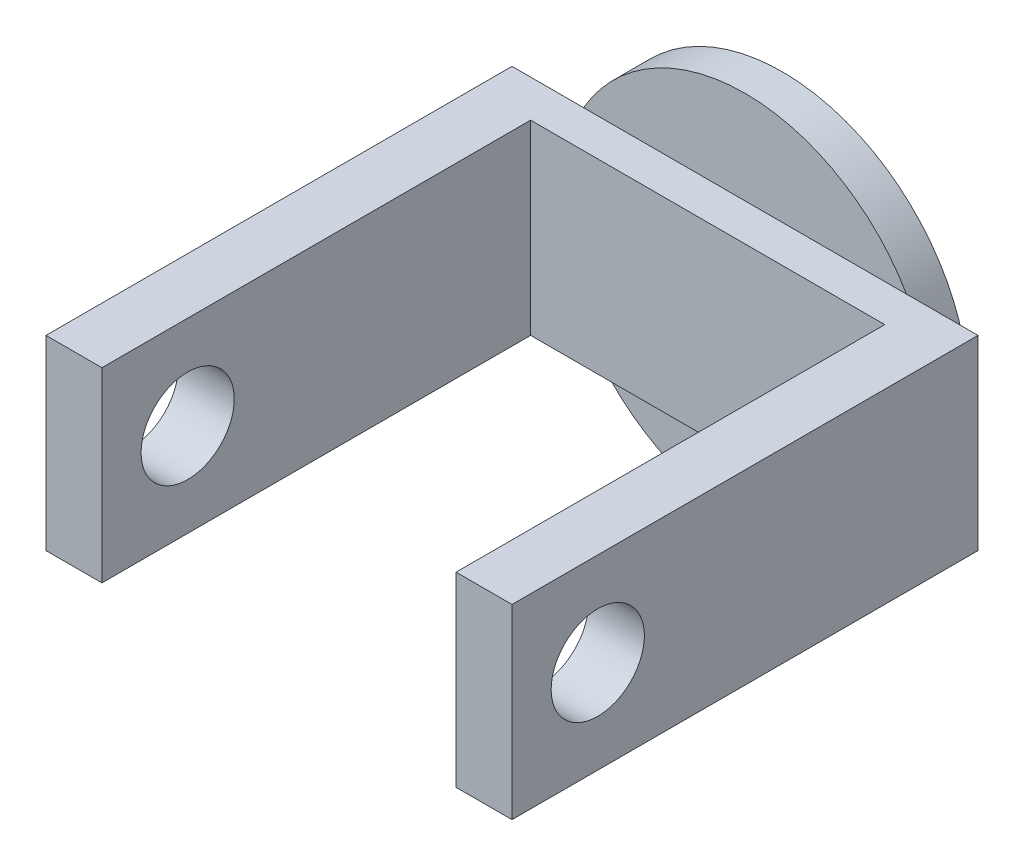
SolidWorks part; units mm, degrees
ref_plane "Front Plane" through (0, 0, 0) normal (0, 0, 1) x (1, 0, 0)
ref_plane "Top Plane" through (0, 0, 0) normal (0, 1, 0) x (1, 0, 0)
ref_plane "Right Plane" through (0, 0, 0) normal (1, 0, 0) x (0, 0, -1)
sketch "Sketch1" plane through (0, 0, 0) normal (0, 0, 1) x (1, 0, 0)
  circle A0 centre (0, 0) radius 50
  dimension "D1" = 100
extrude "Boss-Extrude1" add sketch "Sketch1" along normal blind 10
sketch "Sketch2" plane through (0, 0, 10) normal (0, 0, 1) x (1, 0, 0)
  line L1 (-62.5, -25) -> (62.5, -25)
  line L2 (-62.5, -25) -> (-62.5, 25)
  line L3 (-62.5, 25) -> (62.5, 25)
  line L4 (62.5, -25) -> (62.5, 25)
  dimension "D1" = 62.5
  dimension "D2" = 125
  dimension "D3" = 50
  dimension "D4" = 25
extrude "Boss-Extrude2" add sketch "Sketch2" along normal blind 10
sketch "Sketch3" plane through (0, 0, 20) normal (0, 0, 1) x (1, 0, 0)
  line L0 (-62.5, -25) -> (62.5, -25) construction
  line L1 (-62.5, 25) -> (-47.5, 25)
  line L2 (-62.5, 25) -> (-62.5, -25)
  line L3 (-62.5, -25) -> (-47.5, -25)
  line L4 (-47.5, 25) -> (-47.5, -25)
  line L6 (62.5, 25) -> (47.5, 25)
  line L7 (62.5, 25) -> (62.5, -25)
  line L8 (62.5, -25) -> (47.5, -25)
  line L9 (47.5, 25) -> (47.5, -25)
  dimension "D1" = 95
extrude "Boss-Extrude3" add sketch "Sketch3" along normal blind 115
sketch "Sketch4" plane through (-62.5, 0, 0) normal (-1, 0, 0) x (0, 0, 1)
  circle A0 centre (112, 0) radius 12.5
  point P2 (0, 0)
  dimension "D2" = 25
  dimension "D1" = 112
extrude "Cut-Extrude1" cut sketch "Sketch4" against normal through all
